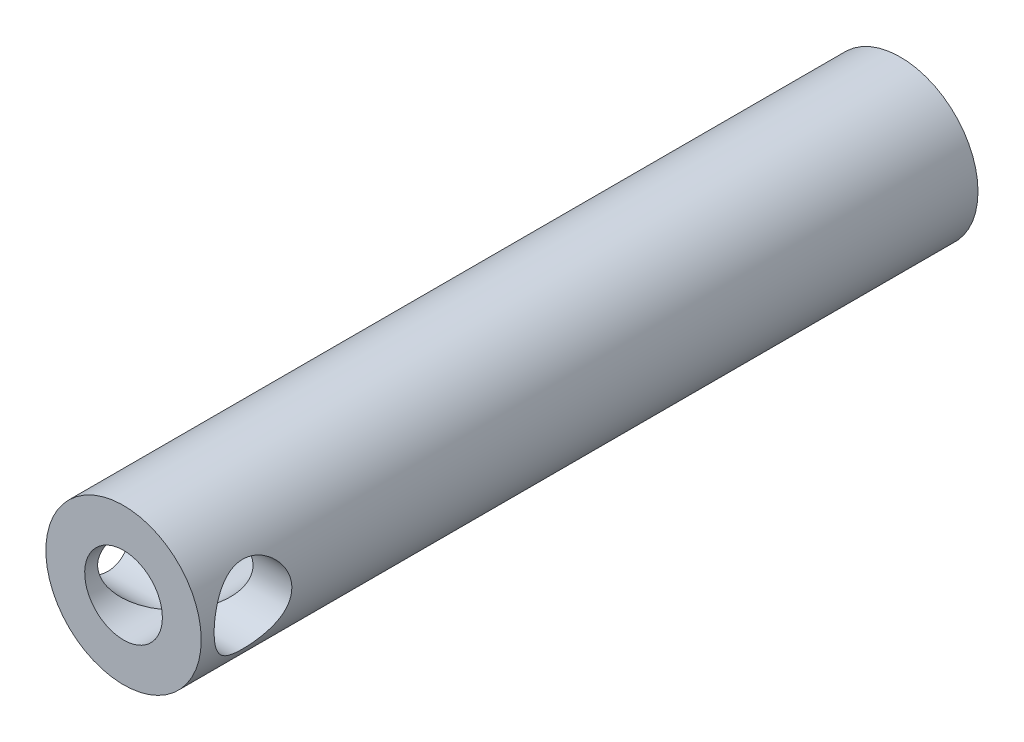
SolidWorks part; units mm, degrees
material "AISI 304"
ref_plane "Front Plane" through (0, 0, 0) normal (0, 0, 1) x (1, 0, 0)
ref_plane "Top Plane" through (0, 0, 0) normal (0, 1, 0) x (1, 0, 0)
ref_plane "Right Plane" through (0, 0, 0) normal (1, 0, 0) x (0, 0, -1)
sketch "Sketch1" plane through (0, 0, 0) normal (0, 0, 1) x (1, 0, 0)
  circle A0 centre (0, 0) radius 15
  circle A1 centre (0, 0) radius 7.5
extrude "Boss-Extrude1" add sketch "Sketch1" along normal blind 150
sketch "Sketch2" plane through (0, 0, 0) normal (1, 0, 0) x (0, 0, -1)
  circle A0 centre (-140, 0) radius 7.5
extrude "Cut-Extrude2" cut sketch "Sketch2" against normal through all and the other way through all
